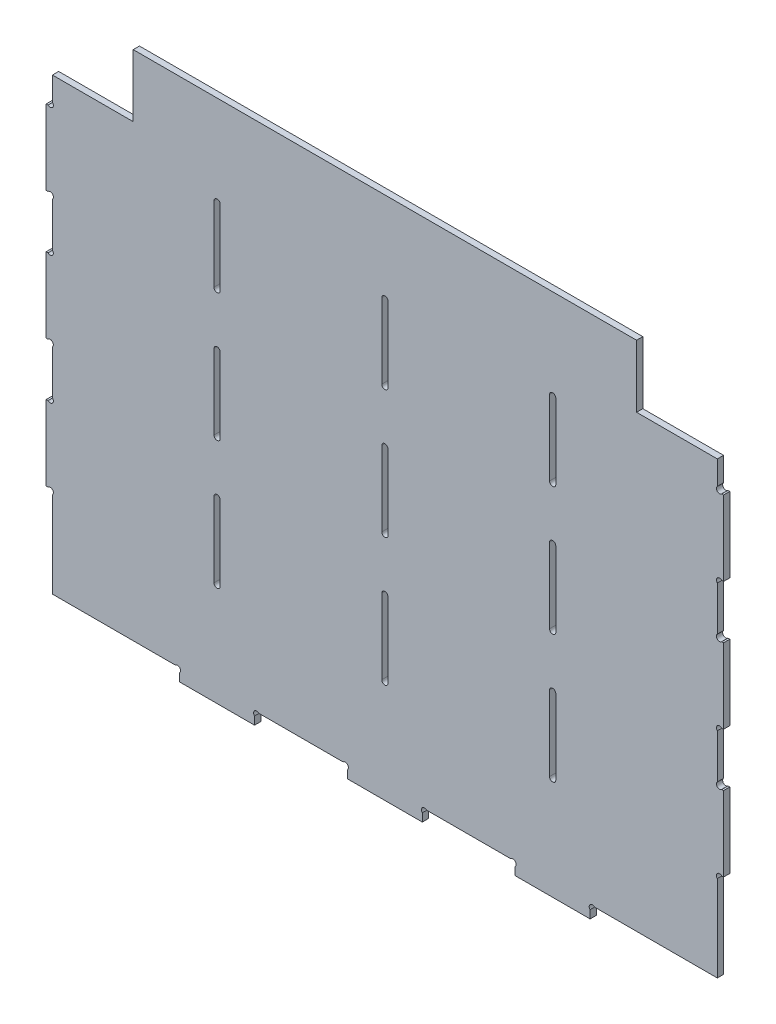
SolidWorks part; units mm, degrees
ref_plane "Front" through (0, 0, 0) normal (0, 0, 1) x (1, 0, 0)
ref_plane "Top" through (0, 0, 0) normal (0, 1, 0) x (1, 0, 0)
ref_plane "Right" through (0, 0, 0) normal (1, 0, 0) x (0, 0, -1)
sketch "Sketch1" plane through (0, 0, 0) normal (0, 0, 1) x (1, 0, 0)
  line L0 (256.125, 263.675) -> (341.5, 263.675) construction
  line L1 (341.5, 263.675) -> (341.5, 0) construction
  line L2 (256.125, 0) -> (341.5, 0) construction
  line L3 (170.75, 0) -> (256.125, 0) construction
  line L4 (256.125, 263.675) -> (256.125, 0) construction
  line L5 (170.75, 263.675) -> (256.125, 263.675) construction
  line L6 (170.75, 263.675) -> (170.75, 0) construction
  line L7 (85.375, 0) -> (170.75, 0) construction
  line L8 (0, 0) -> (85.375, 0) construction
  line L9 (0, 0) -> (0, 263.675) construction
  line L10 (85.375, 263.675) -> (85.375, 0) construction
  line L11 (85.375, 263.675) -> (170.75, 263.675) construction
  line L12 (0, 263.675) -> (85.375, 263.675) construction
  line L13 (256.125, 263.675) -> (341.5, 263.675) construction
  line L14 (341.5, 263.675) -> (341.5, 0) construction
  line L15 (256.125, 0) -> (341.5, 0) construction
  line L16 (170.75, 0) -> (256.125, 0) construction
  line L17 (256.125, 263.675) -> (256.125, 0) construction
  line L18 (170.75, 263.675) -> (256.125, 263.675) construction
  line L19 (170.75, 263.675) -> (170.75, 0) construction
  line L20 (85.375, 0) -> (170.75, 0) construction
  line L21 (0, 0) -> (85.375, 0) construction
  line L22 (0, 0) -> (0, 263.675) construction
  line L23 (85.375, 263.675) -> (85.375, 0) construction
  line L24 (85.375, 263.675) -> (170.75, 263.675) construction
  line L25 (0, 263.675) -> (85.375, 263.675) construction
  line L27 (1.5875, 263.675) -> (339.9125, 263.675)
  line L28 (1.5875, 263.675) -> (1.5875, 3.175)
  line L29 (1.5875, 3.175) -> (339.9125, 3.175)
  line L30 (339.9125, 263.675) -> (339.9125, 3.175)
  point P12 (170.75, 263.675)
  point P13 (341.5, 68.3)
  point P17 (341.5, 133.425)
  point P18 (341.5, 198.55)
  point P22 (0, 68.3)
  point P24 (0, 133.425)
  point P31 (0, 198.55)
  dimension "D1" = 1.5875
  dimension "D2" = 3.175
extrude "Boss-Extrude1" add sketch "Sketch1" along normal mid plane 3.175
sketch "Sketch3" plane through (0, 0, 1.5875) normal (0, 0, 1) x (1, 0, 0)
  line L0 (169.1625, 217.6) -> (169.1625, 179.5)
  line L1 (83.7875, 217.6) -> (86.9625, 217.6) construction
  line L2 (83.7875, 217.6) -> (83.7875, 179.5)
  line L3 (83.7875, 179.5) -> (86.9625, 179.5) construction
  line L4 (86.9625, 217.6) -> (86.9625, 179.5)
  line L5 (83.7875, 217.6) -> (86.9625, 179.5) construction
  line L6 (83.7875, 179.5) -> (86.9625, 217.6) construction
  line L7 (172.3375, 217.6) -> (172.3375, 179.5)
  line L8 (169.1625, 217.6) -> (172.3375, 217.6) construction
  line L9 (169.1625, 179.5) -> (172.3375, 179.5) construction
  line L10 (169.1625, 217.6) -> (172.3375, 179.5) construction
  line L11 (169.1625, 179.5) -> (172.3375, 217.6) construction
  line L12 (254.5375, 217.6) -> (254.5375, 179.5)
  line L13 (257.7125, 217.6) -> (257.7125, 179.5)
  line L14 (254.5375, 217.6) -> (257.7125, 217.6) construction
  line L15 (254.5375, 179.5) -> (257.7125, 179.5) construction
  line L16 (254.5375, 217.6) -> (257.7125, 179.5) construction
  line L17 (254.5375, 179.5) -> (257.7125, 217.6) construction
  line L18 (169.1625, 152.475) -> (169.1625, 114.375)
  line L19 (83.7875, 152.475) -> (83.7875, 114.375)
  line L20 (86.9625, 152.475) -> (86.9625, 114.375)
  line L21 (172.3375, 152.475) -> (172.3375, 114.375)
  line L22 (254.5375, 152.475) -> (254.5375, 114.375)
  line L23 (257.7125, 152.475) -> (257.7125, 114.375)
  line L24 (83.7875, 152.475) -> (86.9625, 152.475) construction
  line L25 (83.7875, 114.375) -> (86.9625, 114.375) construction
  line L26 (83.7875, 152.475) -> (86.9625, 114.375) construction
  line L27 (83.7875, 114.375) -> (86.9625, 152.475) construction
  line L28 (169.1625, 152.475) -> (172.3375, 152.475) construction
  line L29 (169.1625, 114.375) -> (172.3375, 114.375) construction
  line L30 (169.1625, 152.475) -> (172.3375, 114.375) construction
  line L31 (169.1625, 114.375) -> (172.3375, 152.475) construction
  line L32 (254.5375, 152.475) -> (257.7125, 152.475) construction
  line L33 (254.5375, 114.375) -> (257.7125, 114.375) construction
  line L34 (254.5375, 152.475) -> (257.7125, 114.375) construction
  line L35 (254.5375, 114.375) -> (257.7125, 152.475) construction
  line L36 (169.1625, 87.35) -> (169.1625, 49.25)
  line L37 (83.7875, 87.35) -> (83.7875, 49.25)
  line L38 (86.9625, 87.35) -> (86.9625, 49.25)
  line L39 (172.3375, 87.35) -> (172.3375, 49.25)
  line L40 (254.5375, 87.35) -> (254.5375, 49.25)
  line L41 (257.7125, 87.35) -> (257.7125, 49.25)
  line L42 (83.7875, 87.35) -> (86.9625, 87.35) construction
  line L43 (83.7875, 49.25) -> (86.9625, 49.25) construction
  line L44 (83.7875, 87.35) -> (86.9625, 49.25) construction
  line L45 (83.7875, 49.25) -> (86.9625, 87.35) construction
  line L46 (169.1625, 87.35) -> (172.3375, 87.35) construction
  line L47 (169.1625, 49.25) -> (172.3375, 49.25) construction
  line L48 (169.1625, 87.35) -> (172.3375, 49.25) construction
  line L49 (169.1625, 49.25) -> (172.3375, 87.35) construction
  line L50 (254.5375, 87.35) -> (257.7125, 87.35) construction
  line L51 (254.5375, 49.25) -> (257.7125, 49.25) construction
  line L52 (254.5375, 87.35) -> (257.7125, 49.25) construction
  line L53 (254.5375, 49.25) -> (257.7125, 87.35) construction
  arc A0 (83.7875, 217.6) -> (86.9625, 217.6) centre (85.375, 217.6) cw
  arc A1 (83.7875, 179.5) -> (86.9625, 179.5) centre (85.375, 179.5) ccw
  arc A2 (169.1625, 217.6) -> (172.3375, 217.6) centre (170.75, 217.6) cw
  arc A3 (169.1625, 179.5) -> (172.3375, 179.5) centre (170.75, 179.5) ccw
  arc A4 (254.5375, 217.6) -> (257.7125, 217.6) centre (256.125, 217.6) cw
  arc A5 (254.5375, 179.5) -> (257.7125, 179.5) centre (256.125, 179.5) ccw
  arc A6 (83.7875, 152.475) -> (86.9625, 152.475) centre (85.375, 152.475) cw
  arc A7 (83.7875, 114.375) -> (86.9625, 114.375) centre (85.375, 114.375) ccw
  arc A8 (169.1625, 152.475) -> (172.3375, 152.475) centre (170.75, 152.475) cw
  arc A9 (169.1625, 114.375) -> (172.3375, 114.375) centre (170.75, 114.375) ccw
  arc A10 (254.5375, 152.475) -> (257.7125, 152.475) centre (256.125, 152.475) cw
  arc A11 (254.5375, 114.375) -> (257.7125, 114.375) centre (256.125, 114.375) ccw
  arc A12 (83.7875, 87.35) -> (86.9625, 87.35) centre (85.375, 87.35) cw
  arc A13 (83.7875, 49.25) -> (86.9625, 49.25) centre (85.375, 49.25) ccw
  arc A14 (169.1625, 87.35) -> (172.3375, 87.35) centre (170.75, 87.35) cw
  arc A15 (169.1625, 49.25) -> (172.3375, 49.25) centre (170.75, 49.25) ccw
  arc A16 (254.5375, 87.35) -> (257.7125, 87.35) centre (256.125, 87.35) cw
  arc A17 (254.5375, 49.25) -> (257.7125, 49.25) centre (256.125, 49.25) ccw
  point P0 (85.375, 198.55)
  point P2 (256.125, 68.3)
  point P4 (170.75, 68.3)
  point P6 (85.375, 68.3)
  point P8 (85.375, 133.425)
  point P10 (170.75, 133.425)
  point P12 (256.125, 133.425)
  point P14 (256.125, 198.55)
  point P16 (170.75, 198.55)
  point P18 (85.375, 198.55)
  point P24 (170.75, 198.55)
  point P26 (85.375, 133.425)
  point P27 (170.75, 198.55)
  point P34 (256.125, 198.55)
  point P35 (256.125, 198.55)
  point P43 (256.125, 133.425)
  point P44 (170.75, 133.425)
  point P45 (85.375, 133.425)
  point P51 (170.75, 133.425)
  point P53 (170.75, 133.425)
  point P60 (256.125, 133.425)
  point P61 (256.125, 133.425)
  point P68 (85.375, 68.3)
  point P69 (256.125, 68.3)
  point P70 (170.75, 68.3)
  point P71 (85.375, 68.3)
  point P77 (170.75, 68.3)
  point P79 (170.75, 68.3)
  point P86 (256.125, 68.3)
  point P87 (256.125, 68.3)
  dimension "D2" = 3.175
  dimension "D1" = 38.1
  dimension "D3" = 3
  dimension "D4" = 3
extrude "Cut-Extrude1" cut sketch "Sketch3" against normal up to surface (3.175 mm away) up to face at (170.75, 133.425, -1.5875)
sketch "Sketch4" plane through (0, 0, 1.5875) normal (0, 0, 1) x (1, 0, 0)
  line L0 (1.5875, 263.675) -> (1.5875, 3.175) construction
  line L1 (-1.5875, 179.5) -> (1.5875, 179.5)
  line L2 (-1.5875, 179.5) -> (-1.5875, 217.6)
  line L3 (-1.5875, 217.6) -> (1.5875, 217.6)
  line L4 (1.5875, 179.5) -> (1.5875, 217.6)
  line L5 (-1.5875, 179.5) -> (1.5875, 217.6) construction
  line L6 (-1.5875, 217.6) -> (1.5875, 179.5) construction
  line L7 (1.5875, 3.175) -> (339.9125, 3.175) construction
  line L8 (-1.5875, 114.375) -> (1.5875, 114.375)
  line L9 (-1.5875, 114.375) -> (-1.5875, 152.475)
  line L10 (-1.5875, 152.475) -> (1.5875, 152.475)
  line L11 (1.5875, 114.375) -> (1.5875, 152.475)
  line L12 (-1.5875, 114.375) -> (1.5875, 152.475) construction
  line L13 (-1.5875, 152.475) -> (1.5875, 114.375) construction
  line L14 (-1.5875, 49.25) -> (1.5875, 49.25)
  line L15 (-1.5875, 49.25) -> (-1.5875, 87.35)
  line L16 (-1.5875, 87.35) -> (1.5875, 87.35)
  line L17 (1.5875, 49.25) -> (1.5875, 87.35)
  line L18 (-1.5875, 49.25) -> (1.5875, 87.35) construction
  line L19 (-1.5875, 87.35) -> (1.5875, 49.25) construction
  line L20 (66.325, -3.175) -> (104.425, -3.175)
  line L21 (66.325, -3.175) -> (66.325, 3.175)
  line L22 (66.325, 3.175) -> (104.425, 3.175)
  line L23 (104.425, -3.175) -> (104.425, 3.175)
  line L24 (66.325, -3.175) -> (104.425, 3.175) construction
  line L25 (66.325, 3.175) -> (104.425, -3.175) construction
  line L26 (339.9125, 263.675) -> (339.9125, 3.175) construction
  line L27 (151.7, -3.175) -> (189.8, -3.175)
  line L28 (151.7, -3.175) -> (151.7, 3.175)
  line L29 (151.7, 3.175) -> (189.8, 3.175)
  line L30 (189.8, -3.175) -> (189.8, 3.175)
  line L31 (151.7, -3.175) -> (189.8, 3.175) construction
  line L32 (151.7, 3.175) -> (189.8, -3.175) construction
  line L33 (237.075, -3.175) -> (275.175, -3.175)
  line L34 (237.075, -3.175) -> (237.075, 3.175)
  line L35 (237.075, 3.175) -> (275.175, 3.175)
  line L36 (275.175, -3.175) -> (275.175, 3.175)
  line L37 (237.075, -3.175) -> (275.175, 3.175) construction
  line L38 (237.075, 3.175) -> (275.175, -3.175) construction
  line L39 (343.0875, 49.25) -> (339.9125, 49.25)
  line L40 (343.0875, 49.25) -> (343.0875, 87.35)
  line L41 (343.0875, 87.35) -> (339.9125, 87.35)
  line L42 (339.9125, 49.25) -> (339.9125, 87.35)
  line L43 (343.0875, 49.25) -> (339.9125, 87.35) construction
  line L44 (343.0875, 87.35) -> (339.9125, 49.25) construction
  line L46 (343.0875, 114.375) -> (339.9125, 114.375)
  line L47 (343.0875, 114.375) -> (343.0875, 152.475)
  line L48 (343.0875, 152.475) -> (339.9125, 152.475)
  line L49 (339.9125, 114.375) -> (339.9125, 152.475)
  line L50 (343.0875, 114.375) -> (339.9125, 152.475) construction
  line L51 (343.0875, 152.475) -> (339.9125, 114.375) construction
  line L52 (343.0875, 217.6) -> (339.9125, 217.6)
  line L53 (343.0875, 217.6) -> (343.0875, 179.5)
  line L54 (343.0875, 179.5) -> (339.9125, 179.5)
  line L55 (339.9125, 217.6) -> (339.9125, 179.5)
  line L56 (343.0875, 217.6) -> (339.9125, 179.5) construction
  line L57 (343.0875, 179.5) -> (339.9125, 217.6) construction
  point P0 (0, 198.55)
  point P8 (0, 133.425)
  point P14 (0, 68.3)
  point P20 (85.375, 0)
  point P28 (170.75, 0)
  point P34 (256.125, 0)
  point P40 (341.5, 68.3)
  point P48 (341.5, 133.425)
  point P54 (341.5, 198.55)
  dimension "D1" = 38.1
extrude "Boss-Extrude2" add sketch "Sketch4" against normal up to surface (3.175 mm away) up to face at (170.75, 198.55, -1.5875)
sketch "Sketch5" plane through (0, 0, 1.5875) normal (0, 0, 1) x (1, 0, 0)
  line L0 (0, 198.55) -> (0.465, 218.7225) construction
  line L2 (0.465, 218.7225) -> (0.465, 217.6) construction
  line L4 (1.5875, 217.6) -> (-1.5875, 217.6) construction
  line L6 (0.465, 218.7225) -> (1.5875, 218.7225) construction
  line L7 (1.5875, 263.675) -> (1.5875, 3.175) construction
  line L9 (0.465, 218.7225) -> (1.5875, 217.6) construction
  line L10 (1.5875, 198.55) -> (-1.5875, 198.55) construction
  line L12 (-1.5875, 217.6) -> (-1.5875, 179.5) construction
  line L13 (0, 198.55) -> (0.465, 178.3775) construction
  line L15 (0, 133.425) -> (0.465, 153.5975) construction
  line L16 (0, 133.425) -> (0.465, 113.2525) construction
  line L18 (0, 68.3) -> (0.465, 88.4725) construction
  line L19 (0, 68.3) -> (0.465, 48.1275) construction
  line L21 (170.75, 263.675) -> (170.75, 0) construction
  line L23 (341.5, 68.3) -> (341.035, 48.1275) construction
  line L25 (341.5, 68.3) -> (341.035, 88.4725) construction
  line L26 (341.5, 133.425) -> (341.035, 113.2525) construction
  line L27 (341.5, 133.425) -> (341.035, 153.5975) construction
  line L29 (341.5, 198.55) -> (341.035, 178.3775) construction
  line L31 (341.5, 198.55) -> (341.035, 218.7225) construction
  line L32 (85.375, 0) -> (65.2025, 2.0525) construction
  line L33 (65.2025, 2.0525) -> (65.2025, 3.175) construction
  line L35 (1.5875, 3.175) -> (339.9125, 3.175) construction
  line L37 (65.2025, 2.0525) -> (66.325, 2.0525) construction
  line L38 (66.325, 3.175) -> (66.325, -3.175) construction
  line L40 (65.2025, 2.0525) -> (66.325, 3.175) construction
  line L42 (85.375, 3.175) -> (85.375, -3.175) construction
  line L43 (66.325, -3.175) -> (104.425, -3.175) construction
  line L45 (85.375, 0) -> (105.5475, 2.0525) construction
  line L47 (170.75, 0) -> (150.5775, 2.0525) construction
  line L48 (170.75, 0) -> (190.9225, 2.0525) construction
  line L49 (256.125, 0) -> (235.9525, 2.0525) construction
  line L51 (256.125, 0) -> (276.2975, 2.0525) construction
  circle A18 centre (0.465, 218.7225) radius 1.5875
  circle A19 centre (0.465, 178.3775) radius 1.5875
  circle A20 centre (0.465, 153.5975) radius 1.5875
  circle A21 centre (0.465, 113.2525) radius 1.5875
  circle A22 centre (0.465, 88.4725) radius 1.5875
  circle A23 centre (0.465, 48.1275) radius 1.5875
  circle A24 centre (341.035, 48.1275) radius 1.5875
  circle A25 centre (341.035, 88.4725) radius 1.5875
  circle A26 centre (341.035, 113.2525) radius 1.5875
  circle A27 centre (341.035, 153.5975) radius 1.5875
  circle A28 centre (341.035, 178.3775) radius 1.5875
  circle A29 centre (341.035, 218.7225) radius 1.5875
  circle A30 centre (65.2025, 2.0525) radius 1.5875
  circle A31 centre (105.5475, 2.0525) radius 1.5875
  circle A32 centre (150.5775, 2.0525) radius 1.5875
  circle A33 centre (190.9225, 2.0525) radius 1.5875
  circle A34 centre (235.9525, 2.0525) radius 1.5875
  circle A35 centre (276.2975, 2.0525) radius 1.5875
  point P15 (0, 198.55)
  point P59 (85.375, 0)
  dimension "D1" = 1.5875
  dimension "D3" = 3
  dimension "D2" = 45
  dimension "D4" = 1.5875
  dimension "D5" = 45
extrude "Cut-Extrude3" cut sketch "Sketch5" against normal up to surface (3.175 mm away)
sketch "Sketch6" plane through (0, 0, 1.5875) normal (0, 0, 1) x (1, 0, 0)
  line L0 (298.8125, 231.925) -> (341.5, 231.925) construction
  line L1 (298.8125, 263.675) -> (298.8125, 231.925) construction
  line L2 (42.6875, 263.675) -> (42.6875, 231.925) construction
  line L3 (42.6875, 231.925) -> (0, 231.925) construction
  line L4 (298.8125, 231.925) -> (341.5, 231.925)
  line L5 (298.8125, 263.675) -> (298.8125, 231.925)
  line L6 (42.6875, 263.675) -> (42.6875, 231.925)
  line L7 (42.6875, 231.925) -> (0, 231.925)
  line L8 (0, 231.925) -> (0, 263.675)
  line L9 (0, 263.675) -> (42.6875, 263.675)
  line L10 (341.5, 231.925) -> (341.5, 263.675)
  line L11 (341.5, 263.675) -> (298.8125, 263.675)
extrude "Cut-Extrude4" cut sketch "Sketch6" against normal up to surface (3.175 mm away)
equation "\"D1@Sketch1\"=\"acc side wall thickness@FS2-EN-ACC-A-0003-V1, ACCUMULATOR CONTAINER.Assembly\"/2"
equation "\"D2@Sketch1\"=\"acc bottom wall thickness@FS2-EN-ACC-A-0003-V1, ACCUMULATOR CONTAINER.Assembly\"/2"
equation "\"D1@Sketch3\"=\"weld slot length@FS2-EN-ACC-A-0003-V1, ACCUMULATOR CONTAINER.Assembly\""
equation "\"D2@Sketch3\"=\"acc segment side wall thickness@FS2-EN-ACC-A-0003-V1, ACCUMULATOR CONTAINER.Assembly\""
equation "\"D1@Sketch4\"=\"weld slot length@FS2-EN-ACC-A-0003-V1, ACCUMULATOR CONTAINER.Assembly\""
equation "\"D1@Sketch5\"=\"weld teardrop radius@FS2-EN-ACC-A-0003-V1, ACCUMULATOR CONTAINER.Assembly\""
equation "\"D4@Sketch5\"=\"weld teardrop radius@FS2-EN-ACC-A-0003-V1, ACCUMULATOR CONTAINER.Assembly\""
